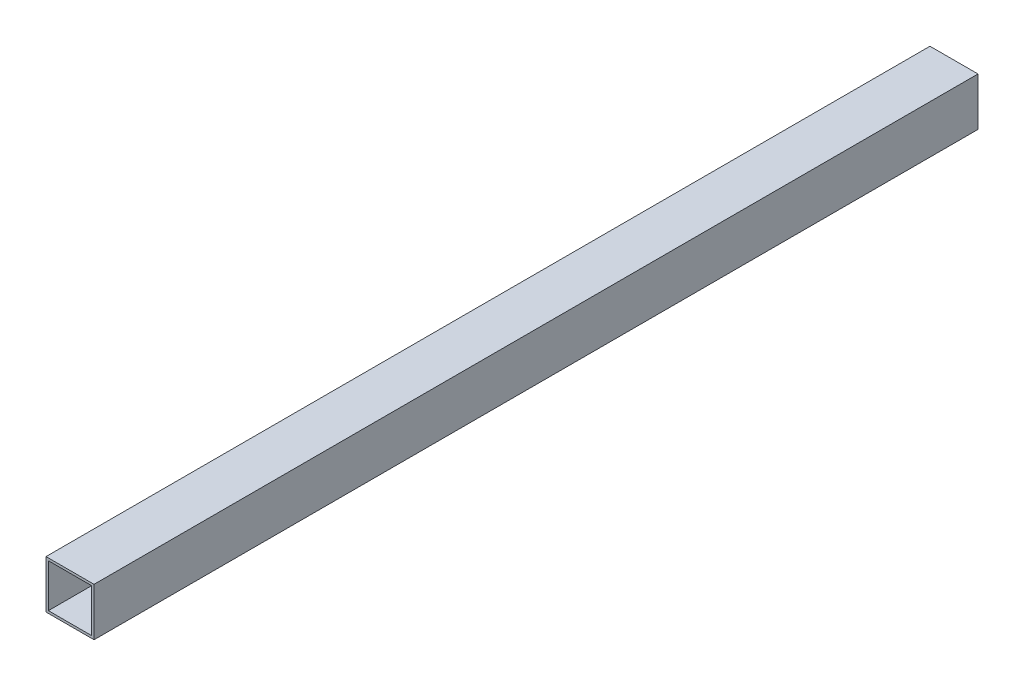
SolidWorks part; units mm, degrees
material "Plain Carbon Steel"
ref_plane "Front Plane" through (0, 0, 0) normal (0, 0, 1) x (1, 0, 0)
ref_plane "Top Plane" through (0, 0, 0) normal (0, 1, 0) x (1, 0, 0)
ref_plane "Right Plane" through (0, 0, 0) normal (1, 0, 0) x (0, 0, -1)
sketch "Sketch1" plane through (0, 0, 0) normal (0, 0, 1) x (1, 0, 0)
  line B0 (-50, -50) -> (50, -50)
  line B1 (-50, -50) -> (-50, 50)
  line B2 (50, -50) -> (50, 50)
  line B3 (-50, 50) -> (50, 50)
  line B4 (-45, -45) -> (45, -45)
  line B5 (-45, -45) -> (-45, 45)
  line B6 (45, -45) -> (45, 45)
  line B7 (-45, 45) -> (45, 45)
sketch_block_instance "10x10x5_profil-1"
sketch_block "10x10x5_profil" parameters "D1"=100, "D2"=100, "D3"=5, "D4"=5
extrude "Boss-Extrude1" add sketch "Sketch1" along normal mid plane 1840
